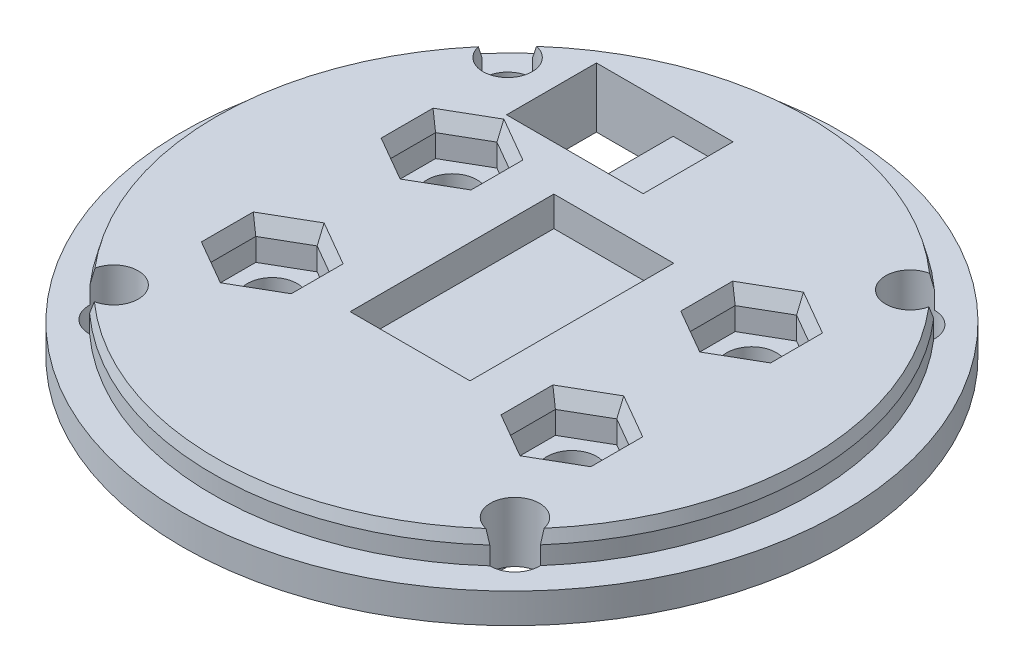
SolidWorks part; units mm, degrees
ref_plane "Спереди" through (0, 0, 0) normal (0, 0, 1) x (1, 0, 0)
ref_plane "Сверху" through (0, 0, 0) normal (0, 1, 0) x (1, 0, 0)
ref_plane "Справа" through (0, 0, 0) normal (1, 0, 0) x (0, 0, -1)
sketch "Эскиз1" plane through (0, 0, 0) normal (0, 1, 0) x (1, 0, 0)
  circle A0 centre (0, 0) radius 55
  dimension "D1" = 110
extrude "Бобышка-Вытянуть1" add sketch "Эскиз1" along normal blind 5
sketch "Эскиз2" plane through (0, 5, 0) normal (0, 1, 0) x (1, 0, 0)
  circle A0 centre (0, 0) radius 49.9
  dimension "D1" = 99.8
extrude "Бобышка-Вытянуть2" add sketch "Эскиз2" along normal blind 5
sketch "Эскиз3" plane through (0, 0, 0) normal (0, -1, 0) x (1, 0, 0)
  line L1 (17.5, -22.5) -> (-17.5, -22.5)
  line L2 (17.5, -22.5) -> (17.5, 22.5)
  line L3 (17.5, 22.5) -> (-17.5, 22.5)
  line L4 (-17.5, -22.5) -> (-17.5, 22.5)
  line L5 (17.5, -22.5) -> (-17.5, 22.5) construction
  line L6 (17.5, 22.5) -> (-17.5, -22.5) construction
  point P0 (0, 0)
  dimension "D1" = 35
  dimension "D2" = 45
extrude "Бобышка-Вытянуть3" add sketch "Эскиз3" along normal blind 25
sketch "Эскиз4" plane through (0, 0, 22.5) normal (0, 0, 1) x (1, 0, 0)
  line L0 (-17.5, 0) -> (17.5, -25) construction
  line L2 (10.1, -17.65) -> (-10.1, -17.65)
  line L3 (10.1, -17.65) -> (10.1, -7.35)
  line L4 (10.1, -7.35) -> (-10.1, -7.35)
  line L5 (-10.1, -17.65) -> (-10.1, -7.35)
  line L6 (10.1, -17.65) -> (-10.1, -7.35) construction
  line L7 (10.1, -7.35) -> (-10.1, -17.65) construction
  point P4 (0, -12.5)
  dimension "D1" = 20.2
  dimension "D2" = 10.3
extrude "Вырез-Вытянуть1" cut sketch "Эскиз4" against normal through all
sketch "Эскиз5" plane through (0, 0, 0) normal (0, -1, 0) x (1, 0, 0)
  line L0 (23.35, -22.85) -> (39.3102, -38.467) construction
  line L5 (-23.35, 22.85) -> (23.35, -22.85) construction
  line L6 (-23.35, -22.85) -> (23.35, 22.85) construction
  line L7 (-23.35, 22.85) -> (-39.3095, 38.4677) construction
  line L8 (23.35, 22.85) -> (39.1401, 38.6401) construction
  line L9 (-23.35, -22.85) -> (-39.3095, -38.4677) construction
  circle A0 centre (0, 0) radius 55 construction
  circle A1 centre (33.5922, -32.8719) radius 4.1
  circle A2 centre (-33.5917, -32.8724) radius 4.1
  circle A3 centre (-33.5917, 32.8724) radius 4.1
  circle A4 centre (33.4832, 32.9832) radius 4.1
  point P0 (0, 0)
  dimension "D3" = 8.2
  dimension "D1" = 46.7
  dimension "D2" = 45.7
  dimension "D4" = 8
  dimension "D5" = 8
  dimension "D6" = 8
  dimension "D7" = 8
extrude "Вырез-Вытянуть2" cut sketch "Эскиз5" against normal through all
sketch "Эскиз6" plane through (0, 10, 0) normal (0, 1, 0) x (1, 0, 0)
  line L0 (0, 0) -> (0.0004, 49.9) construction
  line L1 (0.0002, 28) -> (-17.9998, 28) construction
  arc A0 (33.5133, 36.9712) -> (-33.5128, 36.9717) centre (0, 0) ccw construction
  circle A1 centre (-17.9998, 28) radius 2.75
  dimension "D3" = 5.5
  dimension "D1" = 28
  dimension "D2" = 18
extrude "Вырез-Вытянуть3" cut sketch "Эскиз6" against normal through all
chamfer "Chamfer1" distance 2 angle 15 4 edges at (-0.0824, 10, 49.8999) (-49.9, 10, 0) (0.0004, 10, -49.9) (49.8999, 10, 0.0826)
sketch "Sketch2" plane through (0, -25, 0) normal (0, -1, 0) x (1, 0, 0)
  line L0 (17.5, 0) -> (-17.5652, 0) construction
  line L1 (17.5, -22.5) -> (17.5, 22.5) construction
  line L4 (-17.5652, -22.5) -> (17.5, -22.5)
  line L5 (-17.5652, -22.5) -> (-17.5652, 22.5)
  line L6 (-17.5652, 22.5) -> (17.5, 22.5)
  line L7 (17.5, -22.5) -> (17.5, 22.5)
  line L8 (-17.5652, -22.5) -> (17.5, 22.5) construction
  line L9 (-17.5652, 22.5) -> (17.5, -22.5) construction
  point P6 (-0.0326, 0)
extrude "Cut-Extrude1" cut sketch "Sketch2" against normal blind 12.5
sketch "Sketch4" plane through (0, -7.35, 0) normal (0, -1, 0) x (1, 0, 0)
  line L1 (-35, -22.5) -> (35, -22.5)
  line L2 (-35, -22.5) -> (-35, 22.5)
  line L3 (-35, 22.5) -> (35, 22.5)
  line L4 (35, -22.5) -> (35, 22.5)
  line L5 (-35, -22.5) -> (35, 22.5) construction
  line L6 (-35, 22.5) -> (35, -22.5) construction
  point P0 (0, 0)
  dimension "D1" = 45
  dimension "D2" = 70
extrude "Boss-Extrude1" add sketch "Sketch4" against normal up to surface (5.35 mm away) from offset 2 up to face at (-17.9998, 0, -25.25) offset against normal yes
sketch "Sketch5" plane through (0, -5.35, 0) normal (0, -1, 0) x (1, 0, 0)
  line L0 (25, 22.5) -> (25, -22.5) construction
  line L1 (35, 22.5) -> (17.5, 22.5) construction
  line L2 (17.5, -22.5) -> (35, -22.5) construction
  line L3 (-25, 22.5) -> (-25, -22.5) construction
  line L4 (-17.5, 22.5) -> (-35, 22.5) construction
  line L5 (-35, -22.5) -> (-17.5, -22.5) construction
  line L6 (25, 15) -> (-25, 15) construction
  line L7 (25, -15) -> (-25, -15) construction
  circle A0 centre (25, 15) radius 4.15
  circle A1 centre (-25, 15) radius 4.15
  circle A2 centre (25, -15) radius 4.15
  circle A3 centre (-25, -15) radius 4.15
  point P21 (25, 0)
  dimension "D1" = 8.3
  dimension "D2" = 50
  dimension "D3" = 25
  dimension "D4" = 30
  dimension "D5" = 15
extrude "Cut-Extrude2" cut sketch "Sketch5" against normal through all
sketch "Sketch6" plane through (0, 10, 0) normal (0, 1, 0) x (1, 0, 0)
  line L1 (-18.5048, -11.25) -> (-25, -7.5)
  line L2 (-25, -7.5) -> (-31.4952, -11.25)
  line L3 (-31.4952, -11.25) -> (-31.4952, -18.75)
  line L4 (-31.4952, -18.75) -> (-25, -22.5)
  line L5 (-25, -22.5) -> (-18.5048, -18.75)
  line L6 (-18.5048, -18.75) -> (-18.5048, -11.25)
  line L7 (31.4952, -11.25) -> (25, -7.5)
  line L8 (25, -7.5) -> (18.5048, -11.25)
  line L9 (18.5048, -11.25) -> (18.5048, -18.75)
  line L10 (18.5048, -18.75) -> (25, -22.5)
  line L11 (25, -22.5) -> (31.4952, -18.75)
  line L12 (31.4952, -18.75) -> (31.4952, -11.25)
  line L13 (31.4952, 18.75) -> (25, 22.5)
  line L14 (25, 22.5) -> (18.5048, 18.75)
  line L15 (18.5048, 18.75) -> (18.5048, 11.25)
  line L16 (18.5048, 11.25) -> (25, 7.5)
  line L17 (25, 7.5) -> (31.4952, 11.25)
  line L18 (31.4952, 11.25) -> (31.4952, 18.75)
  line L19 (-18.5048, 18.75) -> (-25, 22.5)
  line L20 (-25, 22.5) -> (-31.4952, 18.75)
  line L21 (-31.4952, 18.75) -> (-31.4952, 11.25)
  line L22 (-31.4952, 11.25) -> (-25, 7.5)
  line L23 (-25, 7.5) -> (-18.5048, 11.25)
  line L24 (-18.5048, 11.25) -> (-18.5048, 18.75)
  circle A0 centre (-25, -15) radius 7.5 construction
  circle A1 centre (25, -15) radius 7.5 construction
  circle A2 centre (25, 15) radius 7.5 construction
  circle A3 centre (-25, 15) radius 7.5 construction
  dimension "D1" = 15
extrude "Cut-Extrude3" cut sketch "Sketch6" against normal blind 6.5
sketch "Sketch7" plane through (0, 10, 0) normal (0, 1, 0) x (1, 0, 0)
  line L1 (-10, -17) -> (10, -17)
  line L2 (-10, -17) -> (-10, 17)
  line L3 (-10, 17) -> (10, 17)
  line L4 (10, -17) -> (10, 17)
  line L5 (-10, -17) -> (10, 17) construction
  line L6 (-10, 17) -> (10, -17) construction
  point P0 (0, 0)
  dimension "D1" = 20
  dimension "D2" = 34
extrude "Cut-Extrude4" cut sketch "Sketch7" against normal blind 5
chamfer "Chamfer2" distance 1 angle 70 24 edges at (-28.2476, 10, 9.375) (-31.4952, 10, 15) (-28.2476, 10, 20.625) (-21.7524, 10, 20.625) (-18.5048, 10, 15) (-21.7524, 10, 9.375) (18.5048, 10, 15) (21.7524, 10, 20.625) (28.2476, 10, 20.625) (31.4952, 10, 15) (28.2476, 10, 9.375) (21.7524, 10, 9.375) (-28.2476, 10, -9.375) (-31.4952, 10, -15) (-28.2476, 10, -20.625) (-21.7524, 10, -20.625) (-18.5048, 10, -15) (-21.7524, 10, -9.375) (21.7524, 10, -9.375) (18.5048, 10, -15) (21.7524, 10, -20.625) (28.2476, 10, -20.625) (31.4952, 10, -15) (28.2476, 10, -9.375)
sketch "Sketch8" plane through (0, 0, 0) normal (0, -1, 0) x (1, 0, 0)
  line L0 (-19, -51.614) -> (-19, 51.614) construction
  line L2 (-25.4, -39.5) -> (-12.6, -39.5)
  line L3 (-25.4, -39.5) -> (-25.4, -24.5)
  line L4 (-25.4, -24.5) -> (-12.6, -24.5)
  line L5 (-12.6, -39.5) -> (-12.6, -24.5)
  line L6 (-25.4, -39.5) -> (-12.6, -24.5) construction
  line L7 (-25.4, -24.5) -> (-12.6, -39.5) construction
  circle A0 centre (0, 0) radius 55 construction
  point P4 (-19, -32)
  point P10 (-19, -33.204)
  dimension "D1" = 19
  dimension "D2" = 15
  dimension "D3" = 12.8
  dimension "D4" = 32
extrude "Cut-Extrude5" cut sketch "Sketch8" against normal through all
sketch "Sketch9" plane through (0, 10, 0) normal (0, 1, 0) x (1, 0, 0)
  line L0 (-12.6, 39.5) -> (-2.6, 39.5)
  line L1 (-2.6, 39.5) -> (-2.6, 24.5)
  line L2 (-2.6, 24.5) -> (-12.6, 24.5)
  line L3 (-12.6, 24.5) -> (-12.6, 39.5)
  dimension "D1" = 10
extrude "Cut-Extrude6" cut sketch "Sketch9" against normal offset from surface (4.2 mm away) 5.8 up to face at (-19, 0, -32)
